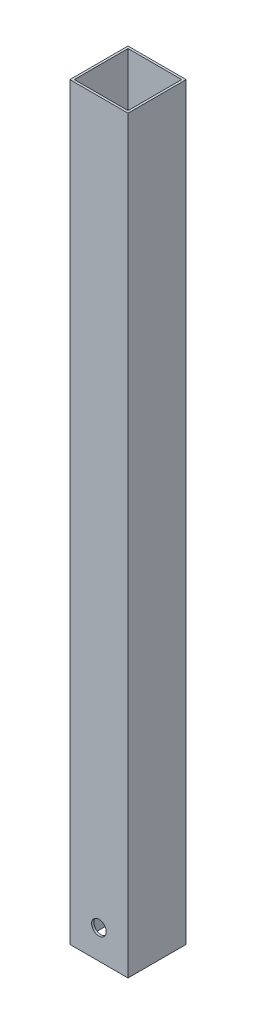
SolidWorks part; units mm, degrees
material "6061-T6 (SS)"
ref_plane "Front Plane" through (0, 0, 0) normal (0, 0, 1) x (1, 0, 0)
ref_plane "Top Plane" through (0, 0, 0) normal (0, 1, 0) x (1, 0, 0)
ref_plane "Right Plane" through (0, 0, 0) normal (1, 0, 0) x (0, 0, -1)
sketch "Sketch1" plane through (0, 0, 0) normal (0, 1, 0) x (1, 0, 0)
  line L0 (-11.7348, -11.7348) -> (11.7348, -11.7348)
  line L1 (-12.7, 12.7) -> (12.7, 12.7)
  line L2 (-12.7, 12.7) -> (-12.7, -12.7)
  line L3 (-12.7, -12.7) -> (12.7, -12.7)
  line L4 (12.7, 12.7) -> (12.7, -12.7)
  line L5 (-12.7, 12.7) -> (12.7, -12.7) construction
  line L6 (-12.7, -12.7) -> (12.7, 12.7) construction
  line L7 (11.7348, 11.7348) -> (11.7348, -11.7348)
  line L8 (-11.7348, 11.7348) -> (11.7348, 11.7348)
  line L9 (-11.7348, 11.7348) -> (-11.7348, -11.7348)
  point P0 (0, 0)
  dimension "D1" = 25.4
  dimension "D2" = 25.4
  dimension "D3" = 0.9652
extrude "Boss-Extrude1" add sketch "Sketch1" along normal blind 327.152
sketch "Sketch3" plane through (0, 0, 12.7) normal (0, 0, 1) x (1, 0, 0)
  line L0 (-12.7, 0) -> (12.7, 0) construction
  line L1 (12.7, 327.152) -> (12.7, 0) construction
  circle A0 centre (0, 12.7) radius 3.175
  dimension "D1" = 6.35
  dimension "D3" = 12.7
  dimension "D2" = 12.7
extrude "Cut-Extrude1" cut sketch "Sketch3" against normal blind 292.1
